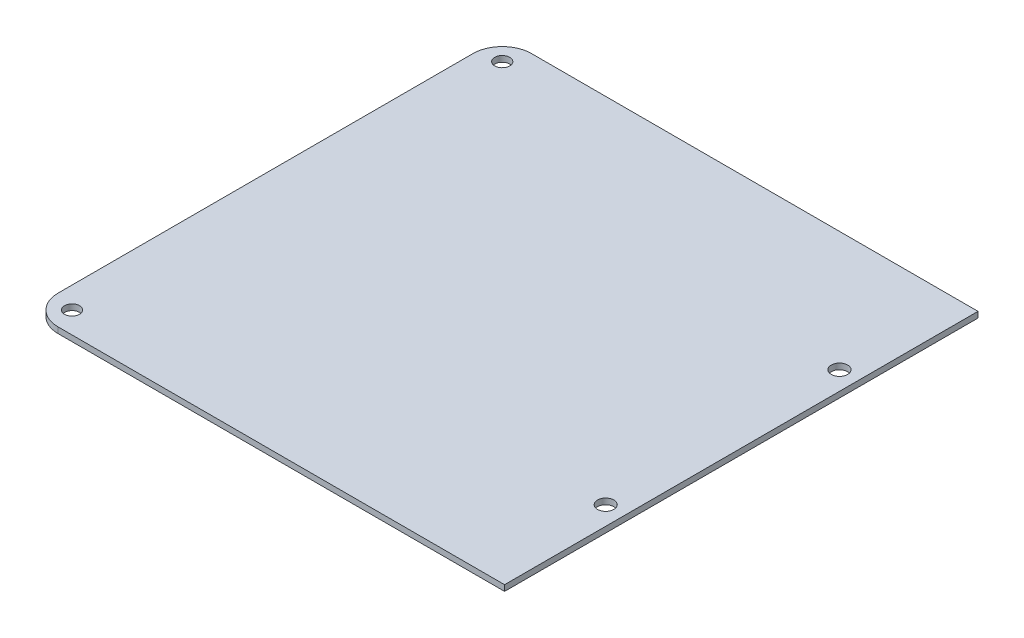
SolidWorks part; units mm, degrees
material "6061-T6 (SS)"
ref_plane "Front Plane" through (0, 0, 0) normal (0, 0, 1) x (1, 0, 0)
ref_plane "Top Plane" through (0, 0, 0) normal (0, 1, 0) x (1, 0, 0)
ref_plane "Right Plane" through (0, 0, 0) normal (1, 0, 0) x (0, 0, -1)
sketch "Sketch1" plane through (0, 0, 0) normal (0, 1, 0) x (1, 0, 0)
  line L1 (-49.8475, -51.435) -> (49.8475, -51.435)
  line L2 (-49.8475, -51.435) -> (-49.8475, 51.435)
  line L3 (-49.8475, 51.435) -> (49.8475, 51.435)
  line L4 (49.8475, -51.435) -> (49.8475, 51.435)
  line L5 (-49.8475, -51.435) -> (49.8475, 51.435) construction
  line L6 (-49.8475, 51.435) -> (49.8475, -51.435) construction
  point P0 (0, 0)
  dimension "D1" = 99.695
  dimension "D2" = 102.87
extrude "Boss-Extrude1" add sketch "Sketch1" along normal blind 2.54
fillet "Fillet2" radius 6.35 2 edges at (-49.8475, 1.27, 51.435) (-49.8475, 1.27, -51.435)
hole_wizard "#4 Clearance Hole1" positions "Sketch3" profile "Sketch4" hole size "#4" standard "ANSI Inch"
sketch "Sketch3" plane through (0, 2.54, 0) normal (0, 1, 0) x (1, 0, 0)
  line L0 (49.8475, 51.435) -> (-43.4975, 51.435) construction
  line L1 (-49.8475, 45.085) -> (-49.8475, -45.085) construction
  line L2 (-43.4975, -51.435) -> (49.8475, -51.435) construction
  point P0 (-45.1485, 46.736)
  point P2 (-45.1485, -46.736)
  dimension "D1" = 4.699
  dimension "D2" = 4.699
  dimension "D3" = 4.699
sketch "Sketch4" plane through (-45.1485, 2.54, -46.736) normal (1, 0, 0) x (0, 0, 1)
  line L0 (0, 0) -> (0, 5.9336)
  line L1 (0, 5.9336) -> (1.6319, 4.953)
  line L2 (1.6319, 4.953) -> (1.6319, 0)
  line L5 (1.6319, 0) -> (0, 0)
  line L10 (0, 5.9336) -> (-1.632, 4.953) construction
  line L11 (0, -6.35) -> (0, 107.95) construction
  dimension "Hole Dia." = 3.2639
  dimension "Hole Depth" = 4.953
  dimension "Drill Angle" = 118
sketch "Sketch5" plane through (49.8475, 0, 0) normal (1, 0, 0) x (0, 0, -1)
  line L0 (51.435, 2.54) -> (51.435, 0) construction
  line L1 (-51.435, 0) -> (51.435, 0)
  line L2 (-51.435, 0) -> (-51.435, 1.27)
  line L3 (-51.435, 1.27) -> (51.435, 1.27)
  line L4 (51.435, 0) -> (51.435, 1.27)
extrude "Cut-Extrude1" cut sketch "Sketch5" against normal blind 4.445
sketch "Sketch6" plane through (49.8475, 0, 0) normal (1, 0, 0) x (0, 0, -1)
  line L1 (-51.435, 2.54) -> (51.435, 2.54)
  line L2 (-51.435, 2.54) -> (-51.435, 1.27)
  line L3 (-51.435, 1.27) -> (51.435, 1.27)
  line L4 (51.435, 2.54) -> (51.435, 1.27)
extrude "Boss-Extrude3" add sketch "Sketch6" along normal blind 3.683
hole_wizard "#4 Clearance Hole2" positions "Sketch7" profile "Sketch8" hole size "#4" standard "ANSI Inch"
sketch "Sketch7" plane through (0, 2.54, 0) normal (0, 1, 0) x (1, 0, 0)
  line L0 (49.4665, 25.4) -> (49.4665, -25.4) construction
  line L1 (0, 0) -> (49.4665, 0) construction
  line L2 (53.5305, 0) -> (45.4025, 0) construction
  line L3 (53.5305, 51.435) -> (53.5305, -51.435) construction
  line L4 (45.4025, 51.435) -> (45.4025, -51.435) construction
  point P0 (49.4665, 25.4)
  point P2 (49.4665, -25.4)
  dimension "D1" = 50.8
sketch "Sketch8" plane through (49.4665, 2.54, -25.4) normal (1, 0, 0) x (0, 0, 1)
  line L0 (0, 0) -> (0, 8.6629)
  line L1 (0, 8.6629) -> (1.778, 7.5946)
  line L2 (1.778, 7.5946) -> (1.778, 0)
  line L5 (1.778, 0) -> (0, 0)
  line L10 (0, 8.6629) -> (-1.778, 7.5946) construction
  line L11 (0, -6.35) -> (0, 107.95) construction
  dimension "Hole Dia." = 3.556
  dimension "Hole Depth" = 7.5946
  dimension "Drill Angle" = 118
sketch "Sketch11" plane through (0, 0, 0) normal (0, -1, 0) x (1, 0, 0)
  line L12 (-46.0375, 43.434) -> (-46.0375, -43.434)
  line L13 (-46.0375, -43.434) -> (-43.1165, -43.434)
  line L14 (-41.8465, -44.704) -> (-41.8465, -47.625)
  line L15 (-41.8465, -47.625) -> (45.4025, -47.625)
  line L16 (45.4025, -51.435) -> (45.4025, 51.435)
  line L17 (45.4025, 51.435) -> (-43.4975, 51.435)
  line L18 (-49.8475, 45.085) -> (-49.8475, -45.085)
  line L19 (-43.4975, -51.435) -> (45.4025, -51.435)
  line L20 (45.4025, -51.435) -> (45.4025, 51.435)
  line L21 (45.4025, 51.435) -> (-43.4975, 51.435)
  line L22 (-49.8475, 45.085) -> (-49.8475, -45.085)
  line L23 (-43.4975, -51.435) -> (45.4025, -51.435)
  line L24 (45.4025, -47.625) -> (45.4025, 47.625)
  line L25 (45.4025, 47.625) -> (-41.8465, 47.625)
  line L26 (-41.8465, 47.625) -> (-41.8465, 44.704)
  line L27 (-43.1165, 43.434) -> (-46.0375, 43.434)
  arc A6 (-43.1165, -43.434) -> (-41.8465, -44.704) centre (-43.1165, -44.704) cw
  arc A7 (-41.8465, 44.704) -> (-43.1165, 43.434) centre (-43.1165, 44.704) cw
  arc A8 (-43.4975, 51.435) -> (-49.8475, 45.085) centre (-43.4975, 45.085) ccw
  arc A9 (-49.8475, -45.085) -> (-43.4975, -51.435) centre (-43.4975, -45.085) ccw
  arc A10 (-43.4975, 51.435) -> (-49.8475, 45.085) centre (-43.4975, 45.085) ccw
  arc A11 (-49.8475, -45.085) -> (-43.4975, -51.435) centre (-43.4975, -45.085) ccw
  dimension "D7" = 1.27
  dimension "D2" = 3.81
  dimension "D3" = 8.001
  dimension "D4" = 8.001
  dimension "D5" = 3.81
  dimension "D6" = 8.001
  dimension "D1" = 0
extrude "Cut-Extrude2" cut sketch "Sketch11" against normal blind 1.27
ref_plane "Plane1" through (0, 1.74, 0) normal (0, 1, 0) x (1, 0, 0)
sketch "Sketch12" plane through (0, 0, 0) normal (0, -1, 0) x (1, 0, 0)
  line L0 (-39.6875, -22.225) -> (-27.8342, -41.275)
  line L1 (-38.4175, -22.225) -> (-26.5642, -41.275)
  line L2 (-26.5642, -41.275) -> (-14.7108, -22.225)
  line L3 (-13.4408, -22.225) -> (-25.2942, -41.275)
  line L4 (-0.3175, -41.275) -> (-12.1708, -22.225)
  line L5 (-13.4408, -22.225) -> (-1.5875, -41.275)
  line L6 (-26.5642, -31.75) -> (-26.5642, -41.275) construction
  line L7 (-32.4908, -31.75) -> (-20.6375, -31.75) construction
  line L8 (-39.6875, -22.225) -> (39.0525, -22.225)
  line L9 (-39.6875, -20.955) -> (39.0525, -20.955)
  line L10 (-27.8342, -41.275) -> (-26.5642, -41.275) construction
  line L11 (-26.5642, -41.275) -> (-25.2942, -41.275) construction
  line L12 (-1.5875, -41.275) -> (-0.3175, -41.275) construction
  line L13 (-13.4408, -22.225) -> (-13.4408, -31.75) construction
  line L14 (-19.3675, -31.75) -> (-7.5142, -31.75) construction
  line L15 (-39.6875, -21.59) -> (-0.3175, -21.59) construction
  line L17 (-36.3116, -41.275) -> (39.0525, -41.275)
  line L18 (39.0525, -41.275) -> (39.0525, 41.275)
  line L19 (39.0525, 41.275) -> (-36.3116, 41.275)
  line L22 (-39.6875, 37.8991) -> (-39.6875, -37.8991)
  line L25 (-0.3175, -21.59) -> (-0.3175, -22.225) construction
  line L26 (39.0525, -41.275) -> (39.0525, 41.275)
  line L27 (39.0525, 41.275) -> (-36.3116, 41.275)
  line L30 (-39.6875, -37.8991) -> (-39.6875, 37.8991)
  line L32 (-36.3116, -41.275) -> (39.0525, -41.275)
  line L33 (0, 0) -> (0, -41.275) construction
  line L34 (-39.6875, -20.955) -> (-39.6875, -22.225)
  line L35 (39.0525, -20.955) -> (39.0525, -22.225)
  line L36 (39.0525, -20.955) -> (27.1992, -1.905)
  line L37 (-0.3175, -41.275) -> (11.5358, -22.225)
  line L38 (12.8058, -22.225) -> (0.9525, -41.275)
  line L39 (12.8058, -22.225) -> (24.6592, -41.275)
  line L40 (25.9292, -41.275) -> (14.0758, -22.225)
  line L41 (37.7825, -22.225) -> (25.9292, -41.275)
  line L42 (39.0525, -22.225) -> (27.1992, -41.275)
  line L43 (37.7825, -20.955) -> (25.9292, -1.905)
  line L44 (25.9292, -1.905) -> (14.0758, -20.955)
  line L45 (12.8058, -20.955) -> (24.6592, -1.905)
  line L46 (12.8058, -20.955) -> (0.9525, -1.905)
  line L47 (-0.3175, -1.905) -> (11.5358, -20.955)
  line L48 (-0.3175, -1.905) -> (-12.1708, -20.955)
  line L49 (-13.4408, -20.955) -> (-1.5875, -1.905)
  line L50 (-26.5642, -1.905) -> (-14.7108, -20.955)
  line L51 (-13.4408, -20.955) -> (-25.2942, -1.905)
  line L52 (-38.4175, -20.955) -> (-26.5642, -1.905)
  line L53 (-39.6875, -20.955) -> (-27.8342, -1.905)
  line L54 (-39.6875, -1.905) -> (39.0525, -1.905)
  line L55 (-39.6875, 0) -> (39.0525, 0)
  arc A4 (-39.6875, 37.8991) -> (-36.3116, 41.275) centre (-43.1165, 44.704) ccw
  arc A5 (-36.3116, -41.275) -> (-39.6875, -37.8991) centre (-43.1165, -44.704) ccw
  arc A6 (-39.6875, 37.8991) -> (-36.3116, 41.275) centre (-43.1165, 44.704) ccw
  arc A7 (-36.3116, -41.275) -> (-39.6875, -37.8991) centre (-43.1165, -44.704) ccw
  dimension "D2" = 1.27
  dimension "D3" = 1.905
  dimension "D1" = 6.35
extrude "Cut-Extrude3" cut sketch "Sketch12" against normal up to surface (1.74 mm away)
mirror "Mirror1" about plane through (0, 0, 0) normal (0, 0, 1) of "Cut-Extrude3"
sketch "Sketch13" plane through (0, 2.54, 0) normal (0, 1, 0) x (1, 0, 0)
  circle A0 centre (-47.9876, 49.5751) radius 5
  arc A1 (-43.4975, 51.435) -> (-49.8475, 45.085) centre (-43.4975, 45.085) ccw construction
  circle A2 centre (-47.9876, -49.5751) radius 5
  arc A3 (-49.8475, -45.085) -> (-43.4975, -51.435) centre (-43.4975, -45.085) ccw construction
  circle A4 centre (53.5305, -51.435) radius 5
  circle A5 centre (53.5305, 51.435) radius 5
  dimension "D1" = 10
extrude "Printing Pads" [suppressed] add sketch "Sketch13" against normal blind 0.4
